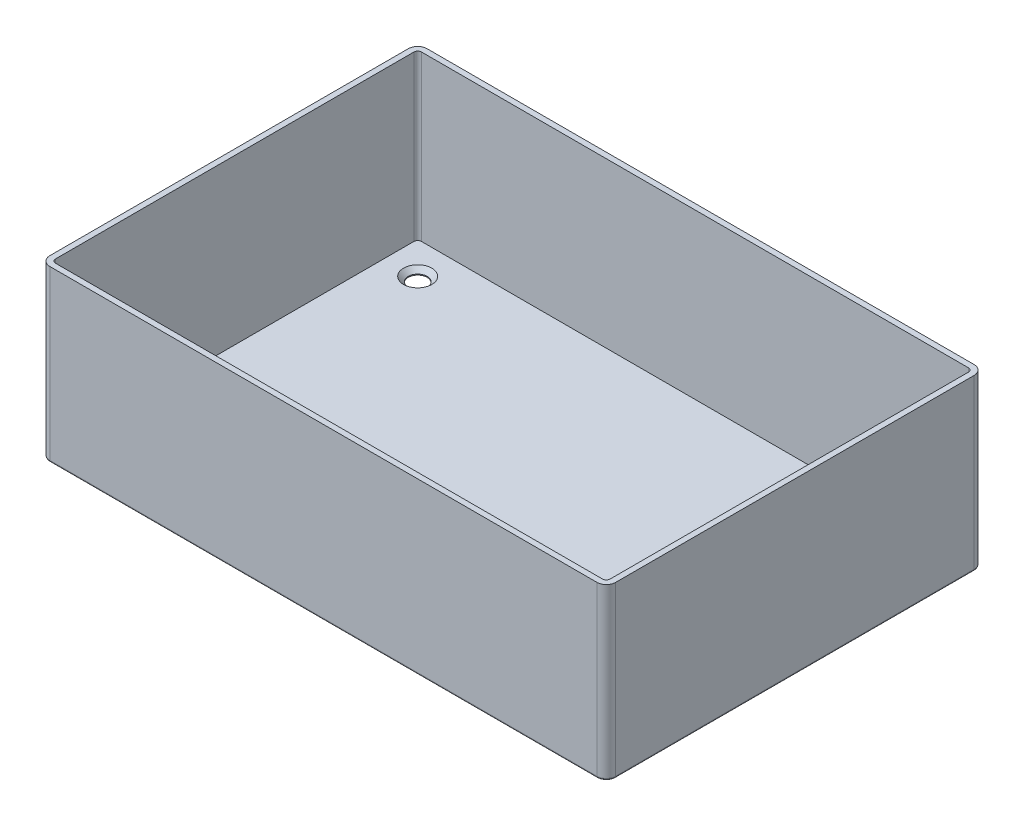
SolidWorks part; units mm, degrees
material "Acrylic (Medium-high impact)"
ref_plane "Front Plane" through (0, 0, 0) normal (0, 0, 1) x (1, 0, 0)
ref_plane "Top Plane" through (0, 0, 0) normal (0, 1, 0) x (1, 0, 0)
ref_plane "Right Plane" through (0, 0, 0) normal (1, 0, 0) x (0, 0, -1)
sketch "Sketch1" plane through (0, 0, 0) normal (0, 1, 0) x (1, 0, 0)
  line L1 (-72.5, -50) -> (72.5, -50)
  line L2 (-75, -47.5) -> (-75, 47.5)
  line L3 (-72.5, 50) -> (72.5, 50)
  line L4 (75, -47.5) -> (75, 47.5)
  line L5 (-75, -50) -> (75, 50) construction
  line L6 (-75, 50) -> (75, -50) construction
  arc A0 (-75, 47.5) -> (-72.5, 50) centre (-72.5, 47.5) cw
  arc A1 (-72.5, -50) -> (-75, -47.5) centre (-72.5, -47.5) cw
  arc A2 (72.5, -50) -> (75, -47.5) centre (72.5, -47.5) ccw
  arc A3 (72.5, 50) -> (75, 47.5) centre (72.5, 47.5) cw
  point P0 (0, 0)
  dimension "D3" = 2.5
  dimension "D1" = 150
  dimension "D2" = 100
extrude "Boss-Extrude1" add sketch "Sketch1" along normal blind 50
shell "Shell1" thickness 1.5
sketch "Sketch2" plane through (0, 1.5, 0) normal (0, 1, 0) x (1, 0, 0)
  line L0 (0, 50) -> (0, -50) construction
  line L1 (72.5, 50) -> (-72.5, 50) construction
  line L2 (-72.5, -50) -> (72.5, -50) construction
  line L3 (-75, 0) -> (75, 0) construction
  line L4 (-75, 47.5) -> (-75, -47.5) construction
  line L5 (75, -47.5) -> (75, 47.5) construction
  circle A0 centre (-65, 40) radius 2.5
  circle A1 centre (65, 40) radius 2.5
  circle A2 centre (65, -40) radius 2.5
  circle A3 centre (-65, -40) radius 2.5
  dimension "D1" = 5
  dimension "D2" = 10
  dimension "D3" = 10
extrude "Cut-Extrude1" cut sketch "Sketch2" against normal blind 50
sketch "Sketch3" plane through (0, 50, 0) normal (0, 1, 0) x (1, 0, 0)
  line L1 (-69.2322, -45.7322) -> (69.2322, -45.7322)
  line L2 (-70.7322, -44.2322) -> (-70.7322, 44.2322)
  line L3 (-69.2322, 45.7322) -> (69.2322, 45.7322)
  line L4 (70.7322, -44.2322) -> (70.7322, 44.2322)
  line L5 (-70.7322, -45.7322) -> (70.7322, 45.7322) construction
  line L6 (-70.7322, 45.7322) -> (70.7322, -45.7322) construction
  arc A0 (75, 47.5) -> (72.5, 50) centre (72.5, 47.5) ccw construction
  arc A1 (-69.2322, -45.7322) -> (-70.7322, -44.2322) centre (-69.2322, -44.2322) cw
  arc A2 (69.2322, -45.7322) -> (70.7322, -44.2322) centre (69.2322, -44.2322) ccw
  arc A3 (69.2322, 45.7322) -> (70.7322, 44.2322) centre (69.2322, 44.2322) cw
  arc A4 (-70.7322, 44.2322) -> (-69.2322, 45.7322) centre (-69.2322, 44.2322) cw
  point P0 (0, 0)
  dimension "D1" = 1.5
extrude "Cut-Extrude2" cut sketch "Sketch3" against normal blind 5 draft 0.5 flip side to cut
fillet "Fillet1" radius 0.5 8 edges at (74.2678, 0, 49.2678) (74.2678, 0, -49.2678) (-74.2678, 0, -49.2678) (-74.2678, 0, 49.2678) (-75, 0, 0) (0, 0, -50) (75, 0, 0) (0, 0, 50)
chamfer "Chamfer1" distance 1.25 angle 45 4 edges at (-65, 1.5, 37.5) (65, 1.5, 42.5) (65, 1.5, -42.5) (-65, 1.5, -37.5)
